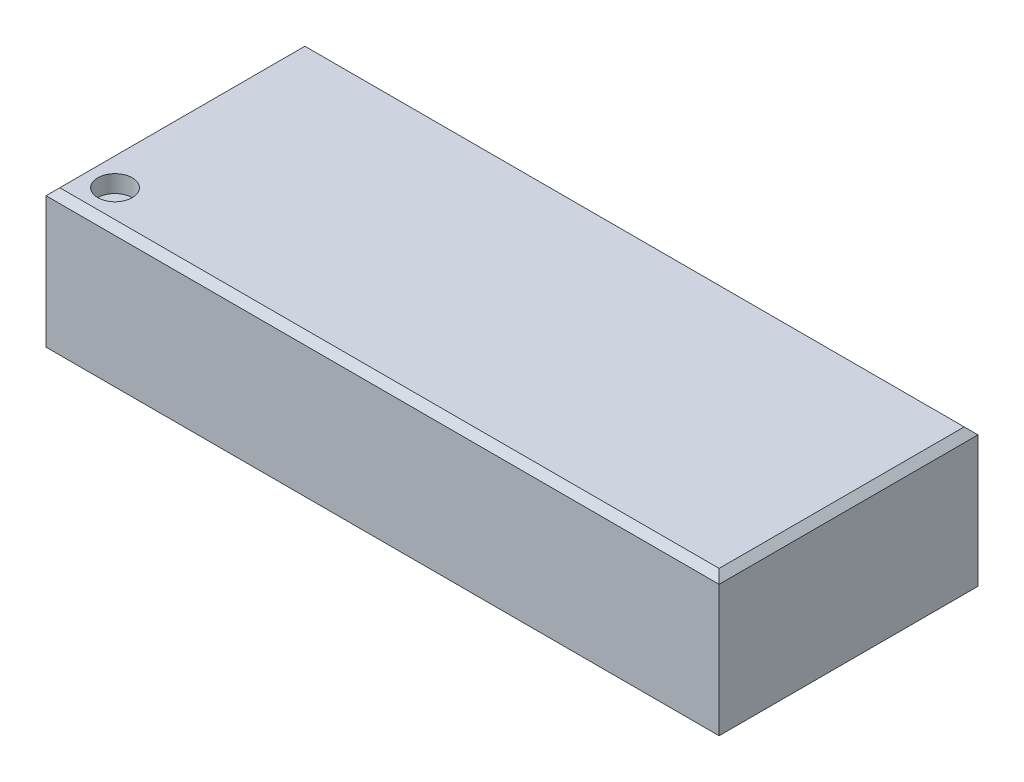
SolidWorks part; units mm, degrees
ref_plane "Plan de face" through (0, 0, 0) normal (0, 0, 1) x (1, 0, 0)
ref_plane "Plan de dessus" through (0, 0, 0) normal (0, 1, 0) x (1, 0, 0)
ref_plane "Plan de droite" through (0, 0, 0) normal (1, 0, 0) x (0, 0, -1)
sketch "Esquisse1" plane through (0, 0, 0) normal (0, 1, 0) x (1, 0, 0)
  line L0 (-6.2355, 0) -> (6.0843, 0) construction
  line L1 (0, 4.4782) -> (0, -3.2689) construction
  line L3 (-4.875, 1.875) -> (4.875, 1.875)
  line L4 (-4.875, 1.875) -> (-4.875, -1.875)
  line L5 (-4.875, -1.875) -> (4.875, -1.875)
  line L6 (4.875, 1.875) -> (4.875, -1.875)
  dimension "D1" = 9.75
  dimension "D2" = 3.75
extrude "Boss.-Extru.1" add sketch "Esquisse1" along normal blind 2
sketch "Esquisse2" plane through (0, 2, 0) normal (0, 1, 0) x (1, 0, 0)
  line L0 (-4.875, -1.875) -> (4.875, -1.875) construction
  line L1 (-4.875, 1.875) -> (-4.875, -1.875) construction
  circle A0 centre (-4.375, -1.375) radius 0.25
  dimension "D1" = 0.5
  dimension "D2" = 0.5
  dimension "D3" = 0.5
extrude "Enlèv. mat.-Extru.1" cut sketch "Esquisse2" against normal blind 0.25
chamfer "Chanfrein1" distance 0.1 angle 45 4 edges at (4.875, 2, 0) (0, 2, 1.875) (0, 2, -1.875) (-4.875, 2, 0)
